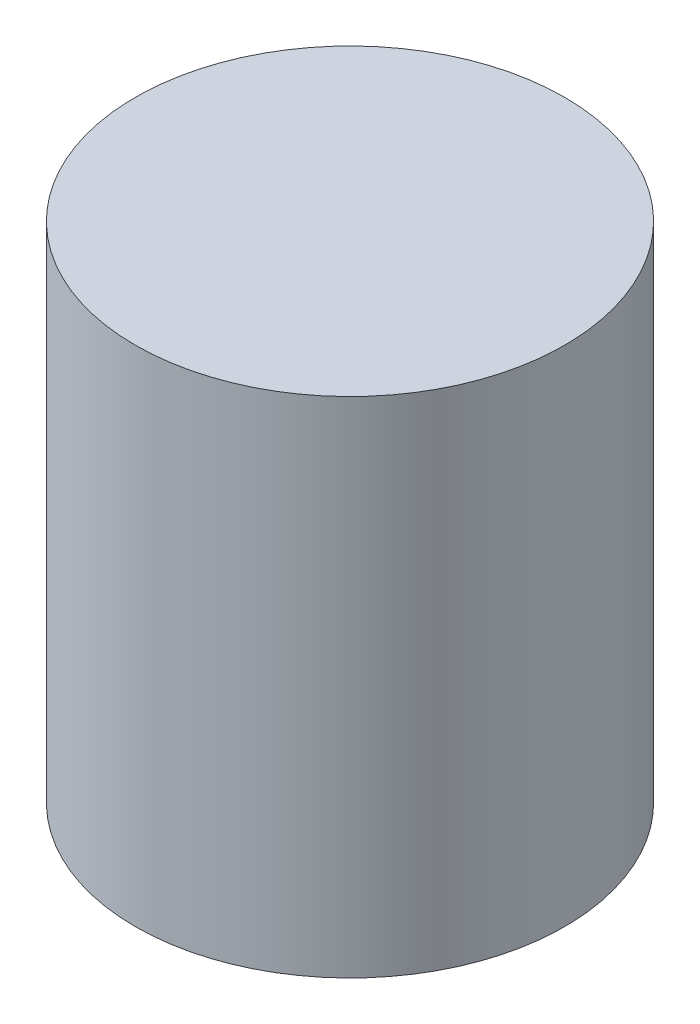
SolidWorks part; units mm, degrees
ref_plane "정면" through (0, 0, 0) normal (0, 0, 1) x (1, 0, 0)
ref_plane "윗면" through (0, 0, 0) normal (0, 1, 0) x (1, 0, 0)
ref_plane "우측면" through (0, 0, 0) normal (1, 0, 0) x (0, 0, -1)
sketch "스케치1" plane through (0, 0, 0) normal (0, 1, 0) x (1, 0, 0)
  circle A0 centre (0, 0) radius 3.05
  circle A1 centre (0, 0) radius 4.05
  dimension "D1" = 6.1
  dimension "D2" = 1
extrude "보스-돌출1" add sketch "스케치1" along normal blind 6
sketch "스케치2" plane through (0, 6, 0) normal (0, 1, 0) x (1, 0, 0)
  circle A0 centre (0, 0) radius 4.05 construction
  circle A1 centre (0, 0) radius 4.05
extrude "보스-돌출2" add sketch "스케치2" along normal blind 3.5
sketch "스케치5" plane through (0, 9.5, 0) normal (0, 1, 0) x (1, 0, 0)
  line L0 (-1.7204, -0.97) -> (1.7204, -0.97)
  line L1 (-4.455, 0) -> (4.455, 0) construction
  circle A0 centre (0, 0) radius 1.975
  dimension "D1" = 3.95
  dimension "D2" = 0.97
extrude "보스-돌출5" [suppressed] add sketch "스케치5" along normal blind 13 contours L0 A0
